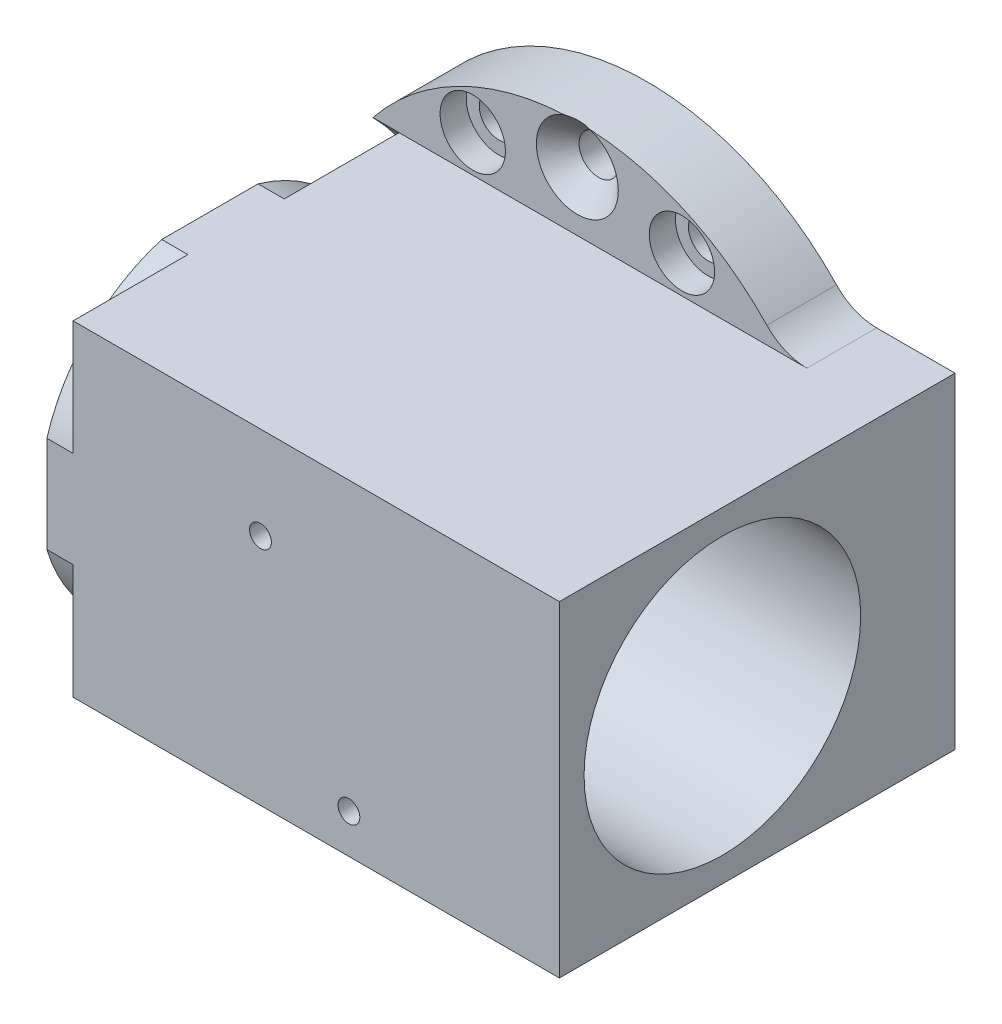
SolidWorks part; units mm, degrees
ref_plane "Front Plane" through (0, 0, 0) normal (0, 0, 1) x (1, 0, 0)
ref_plane "Top Plane" through (0, 0, 0) normal (0, 1, 0) x (1, 0, 0)
ref_plane "Right Plane" through (0, 0, 0) normal (1, 0, 0) x (0, 0, -1)
ref_plane "Plane1" through (0, 0, 8) normal (0, 0, 1) x (1, 0, 0)
sketch "Sketch1" plane through (0, 0, 8) normal (0, 0, 1) x (1, 0, 0)
  line L0 (-23.4587, 18.7) -> (-23.4587, -18.7)
  line L1 (23.4587, -18.7) -> (35.3413, -18.7)
  line L2 (35.3413, -18.7) -> (35.3413, 18.7)
  line L3 (35.3413, 18.7) -> (23.4587, 18.7)
  arc A0 (-23.4587, -18.7) -> (23.4587, -18.7) centre (0, 0) ccw
  arc A1 (23.4587, 18.7) -> (-23.4587, 18.7) centre (0, 0) ccw
extrude "Boss-Extrude1" add sketch "Sketch1" against normal blind 8
ref_plane "Plane2" through (-23.4587, 0, 0) normal (-1, 0, 0) x (0, -1, 0)
ref_plane "Plane3" through (-20.4587, 0, 0) normal (1, 0, 0) x (0, 0, -1)
sketch "Sketch3" plane through (-20.4587, 0, 0) normal (1, 0, 0) x (0, 0, -1)
  line L0 (-8, 18.7) -> (-8, -18.7)
  arc A0 (-8, -18.7) -> (-8, 18.7) centre (-26.7, 0) ccw
extrude "Cut-Extrude1" cut sketch "Sketch3" against normal up to surface up to plane "Plane2"
sketch "Sketch4" plane through (0, 0, 8) normal (0, 0, 1) x (1, 0, 0)
  line L0 (-20.4587, -18.7) -> (-20.4587, 18.7)
  line L1 (-20.4587, 18.7) -> (35.3413, 18.7)
  line L2 (35.3413, 18.7) -> (35.3413, -18.7)
  line L3 (35.3413, -18.7) -> (-20.4587, -18.7)
extrude "Boss-Extrude2" add sketch "Sketch4" along normal blind 37.4
sketch "Sketch5" plane through (-20.4587, 0, 0) normal (-1, 0, 0) x (0, 0, 1)
  line L0 (21.1719, 18.7) -> (45.4, 18.7)
  line L1 (45.4, 18.7) -> (45.4, -18.7)
  line L2 (45.4, -18.7) -> (21.1719, -18.7)
  arc A0 (21.1719, -18.7) -> (21.1719, 18.7) centre (26.7, 0) cw
extrude "Boss-Extrude3" add sketch "Sketch5" along normal blind 3
sketch "Sketch6" plane through (-23.4587, 0, 0) normal (-1, 0, 0) x (0, 0, 1)
  line L0 (45.4, -18.7) -> (45.4, -5.5281)
  line L1 (32.2281, -18.7) -> (45.4, -18.7)
  arc A0 (45.4, -5.5281) -> (32.2281, -18.7) centre (26.7, 0) cw
extrude "Cut-Extrude2" cut sketch "Sketch6" against normal blind 3
sketch "Sketch7" plane through (-23.4587, 0, 0) normal (-1, 0, 0) x (0, 0, 1)
  line L0 (45.4, 18.7) -> (32.2281, 18.7)
  line L1 (45.4, 5.5281) -> (45.4, 18.7)
  arc A0 (32.2281, 18.7) -> (45.4, 5.5281) centre (26.7, 0) cw
extrude "Cut-Extrude3" cut sketch "Sketch7" against normal blind 3
ref_plane "Plane4" through (0, 0, 26.7) normal (0, 0, 1) x (1, 0, 0)
sketch "Sketch8" plane through (0, 0, 26.7) normal (0, 0, 1) x (1, 0, 0)
  line L0 (-23.4587, 15.8686) -> (-23.4587, 0)
  line L1 (-23.4587, 0) -> (35.3413, 0)
  line L2 (35.3413, 0) -> (35.3413, 15.8687)
  line L3 (35.3413, 15.8687) -> (9.9413, 15.8687)
  line L4 (9.9413, 15.8687) -> (9.9413, 13.5)
  line L5 (9.9413, 13.5) -> (1.9413, 13.5)
  line L6 (1.9413, 13.5) -> (1.9413, 15.8686)
  line L7 (1.9413, 15.8686) -> (-23.4587, 15.8686)
  line L8 (-23.4587, 0) -> (35.3413, 0) construction
revolve "Cut-Revolve1" cut sketch "Sketch8" angle 360 about L8
hole_wizard "CSK for #8 Flat Head Machine Screw (100)1" positions "Sketch10" profile "Sketch9" countersink size "#8" standard "ANSI Inch"
sketch "Sketch10" plane through (0, 0, 8) normal (0, 0, 1) x (1, 0, 0)
  point P0 (0, 25.5)
  point P1 (0, -25.5)
sketch "Sketch9" plane through (0, 25.5, 8) normal (1, 0, 0) x (0, -1, 0)
  line L0 (0, 0) -> (0, 8)
  line L1 (0, 8) -> (2.25, 8)
  line L2 (2.25, 8) -> (2.25, 2.45)
  line L3 (2.25, 2.45) -> (4.7, 0)
  line L5 (4.7, 0) -> (0, 0)
  line L6 (-2.25, 2.45) -> (-4.7, 0) construction
  line L11 (0, -6.35) -> (0, 107.95) construction
  dimension "Thru Hole Dia." = 4.5
  dimension "Thru Hole Depth" = 8
  dimension "Near C'Sink Dia." = 9.4
  dimension "Near C'Sink Angle" = 90
hole_wizard "#4 Clearance Hole1" positions "Sketch12" profile "Sketch11" hole size "#4" standard "ANSI Inch"
sketch "Sketch12" plane through (0, -18.7, 0) normal (0, -1, 0) x (-1, 0, 0)
  point P0 (12.4587, -39.4)
  point P1 (-29.4413, -39.4)
  point P2 (-29.4413, -5.9)
sketch "Sketch11" plane through (-12.4587, -18.7, 39.4) normal (1, 0, 0) x (0, 0, -1)
  line L0 (0, 0) -> (0, 6)
  line L1 (0, 6) -> (1.65, 6)
  line L2 (1.65, 6) -> (1.65, 0)
  line L5 (1.65, 0) -> (0, 0)
  line L10 (0, 6) -> (-1.65, 6) construction
  line L11 (0, -6.35) -> (0, 107.95) construction
  dimension "Hole Dia." = 3.3
  dimension "Hole Depth" = 6
  dimension "Drill Angle" = 180
hole_wizard "CBORE for #8 Binding Head Machine Screw1" positions "Sketch14" profile "Sketch13" counterbore size "#8" standard "ANSI Inch"
sketch "Sketch14" plane through (0, 0, 8) normal (0, 0, 1) x (1, 0, 0)
  point P0 (12, 22.95)
  point P1 (-12, 22.95)
  point P2 (-12, -22.95)
  point P3 (12, -22.95)
sketch "Sketch13" plane through (12, 22.95, 8) normal (1, 0, 0) x (0, -1, 0)
  line L0 (0, 0) -> (0, 8)
  line L1 (0, 8) -> (2.25, 8)
  line L3 (2.25, 8) -> (2.25, 3)
  line L4 (2.25, 3) -> (3.75, 3)
  line L5 (3.75, 3) -> (3.75, 0)
  line L7 (3.75, 0) -> (0, 0)
  line L11 (0, -6.35) -> (0, 107.95) construction
  dimension "Thru Hole Dia." = 4.5
  dimension "Thru Hole Depth" = 8
  dimension "C'Bore Dia." = 7.5
  dimension "C'Bore Depth" = 3
hole_wizard "#2 Clearance Hole1" positions "Sketch16" profile "Sketch15" hole size "#2" standard "ANSI Inch"
sketch "Sketch16" plane through (0, 0, 45.4) normal (0, 0, 1) x (1, 0, 0)
  point P0 (-0.8087, 14.63)
sketch "Sketch15" plane through (-0.8087, 14.63, 45.4) normal (1, 0, 0) x (0, -1, 0)
  line L0 (0, 0) -> (0, 6)
  line L1 (0, 6) -> (1.25, 6)
  line L2 (1.25, 6) -> (1.25, 0)
  line L5 (1.25, 0) -> (0, 0)
  line L10 (0, 6) -> (-1.25, 6) construction
  line L11 (0, -6.35) -> (0, 107.95) construction
  dimension "Hole Dia." = 2.5
  dimension "Hole Depth" = 6
  dimension "Drill Angle" = 180
hole_wizard "#2 Clearance Hole2" positions "Sketch18" profile "Sketch17" hole size "#2" standard "ANSI Inch"
sketch "Sketch18" plane through (0, 0, 45.4) normal (0, 0, 1) x (1, 0, 0)
  point P0 (15.9651, -3.2)
sketch "Sketch17" plane through (15.9651, -3.2, 45.4) normal (1, 0, 0) x (0, -1, 0)
  line L0 (0, 0) -> (0, 3.1573)
  line L1 (0, 3.1573) -> (1.25, 3.1573)
  line L2 (1.25, 3.1573) -> (1.25, 0)
  line L5 (1.25, 0) -> (0, 0)
  line L11 (0, -6.35) -> (0, 107.95) construction
  dimension "Thru Hole Dia." = 2.5
  dimension "Thru Hole Depth" = 3.1573
fillet "Fillet1" radius 6.35 1 edges at (23.4587, 18.7, 4)
sketch "Sketch20" plane through (0, 0, 45.4) normal (0, 0, 1) x (1, 0, 0)
  line L0 (35.3413, 18.7) -> (-20.4587, 18.7) construction
  line L1 (-20.4587, -18.7) -> (35.3413, -18.7) construction
  line L2 (-23.4587, 18.7) -> (-23.4587, 5.5281) construction
  point P0 (1.0413, 8.0737)
  point P1 (11.1917, -14.199)
  dimension "D1" = 10.6263
  dimension "D2" = 4.501
  dimension "D3" = 24.4766
  dimension "D4" = 24.5
hole_wizard "M3x0.5 Tapped Hole1" positions "3DSketch1" profile "Sketch23" tap size "M3x0.5" standard "ANSI Metric"
sketch3d "3DSketch1"
  point P0 (1.0413, 8.0737, 45.4)
  point P3 (11.1917, -14.199, 45.4)
sketch "Sketch23" plane through (1.0413, 8.0737, 45.4) normal (1, 0, 0) x (0, -1, 0)
  line L0 (0, 0) -> (0, 4.7511)
  line L1 (0, 4.7511) -> (1.25, 4)
  line L2 (1.25, 4) -> (1.25, 0)
  line L5 (1.25, 0) -> (0, 0)
  line L10 (0, 4.7511) -> (-1.25, 4) construction
  line L11 (0, -6.35) -> (0, 107.95) construction
  dimension "Tap Drill Dia." = 2.5
  dimension "Tap Drill Depth" = 4
  dimension "Drill Angle" = 118
cosmetic thread "Hole Thread1" parameters "D1"=4, "D2"=3
cosmetic thread "Hole Thread2" parameters "D1"=4, "D2"=3
fillet "Fillet2" radius 6.35 1 edges at (23.4587, -18.7, 4)
